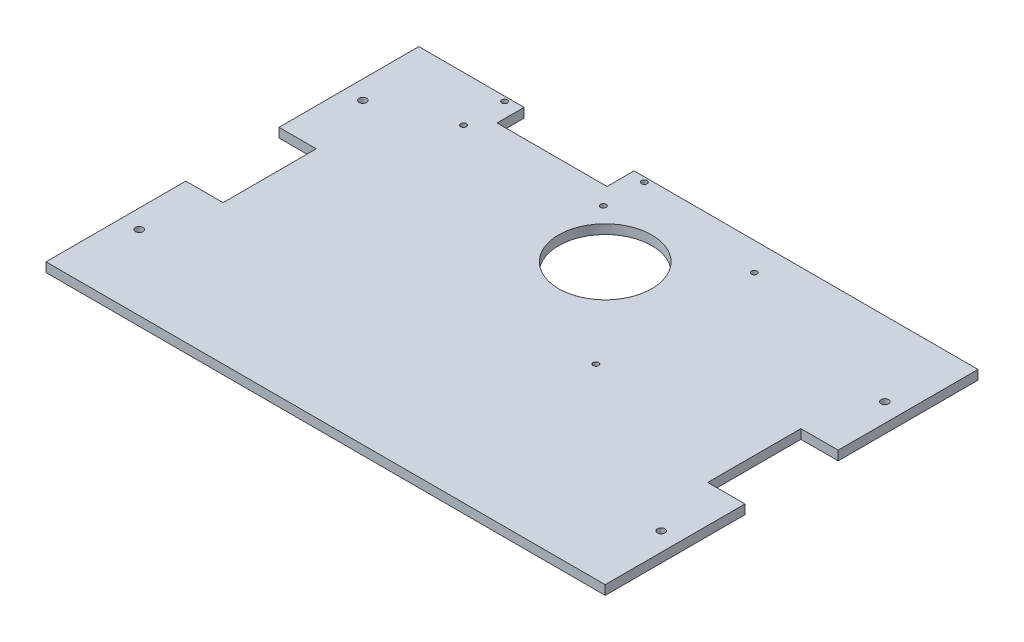
SolidWorks part; units mm, degrees
material "Glass"
ref_plane "前视基准面" through (0, 0, 0) normal (0, 0, 1) x (1, 0, 0)
ref_plane "上视基准面" through (0, 0, 0) normal (0, 1, 0) x (1, 0, 0)
ref_plane "右视基准面" through (0, 0, 0) normal (1, 0, 0) x (0, 0, -1)
sketch "Sketch1" plane through (0, 0, 0) normal (0, 1, 0) x (1, 0, 0)
  line L1 (-150, 100) -> (150, 100)
  line L2 (-150, 100) -> (-150, -100)
  line L3 (-150, -100) -> (150, -100)
  line L4 (150, 100) -> (150, -100)
  line L5 (-150, 100) -> (150, -100) construction
  line L6 (-150, -100) -> (150, 100) construction
  point P0 (0, 0)
  dimension "D1" = 200
  dimension "D2" = 300
extrude "Boss-Extrude1" add sketch "Sketch1" along normal blind 5
sketch "Sketch2" plane through (0, 5, 0) normal (0, 1, 0) x (1, 0, 0)
  line L0 (-140, 100) -> (-140, -100) construction
  line L1 (150, 100) -> (-150, 100) construction
  line L2 (-150, -100) -> (150, -100) construction
  line L3 (-150, -90) -> (150, -90) construction
  line L4 (-150, 100) -> (-150, -100) construction
  line L5 (150, -100) -> (150, 100) construction
  line L6 (0, 0) -> (0, 100) construction
  line L7 (0, 0) -> (150, 0) construction
  line L8 (140, 100) -> (140, -100) construction
  circle A0 centre (-140, 0) radius 2
  circle A1 centre (-140, 60) radius 2
  circle A5 centre (-140, -60) radius 2
  circle A7 centre (140, -60) radius 2
  circle A8 centre (140, 60) radius 2
  circle A9 centre (140, 0) radius 2
  circle A13 centre (0, 50) radius 25
  dimension "D3" = 4
  dimension "D4" = 4
  dimension "D5" = 50
  dimension "D8" = 60
  dimension "D1" = 10
  dimension "D2" = 10
extrude "Cut-Extrude2" cut sketch "Sketch2" against normal through all
sketch "Sketch4" plane through (0, 5, 0) normal (0, 1, 0) x (1, 0, 0)
  line L0 (150, 100) -> (-150, 100) construction
  line L1 (-26.5, 97.5) -> (-101.5, 97.5) construction
  line L2 (-26.5, 97.5) -> (-26.5, 75.5) construction
  line L3 (-26.5, 75.5) -> (-101.5, 75.5) construction
  line L4 (-101.5, 97.5) -> (-101.5, 75.5) construction
  line L5 (-26.5, 97.5) -> (-101.5, 75.5) construction
  line L6 (-26.5, 75.5) -> (-101.5, 97.5) construction
  line L7 (-150, 100) -> (-150, -100) construction
  circle A0 centre (-101.5, 97.5) radius 1.5
  circle A1 centre (-26.5, 97.5) radius 1.5
  circle A2 centre (-26.5, 75.5) radius 1.5
  circle A3 centre (-101.5, 75.5) radius 1.5
  point P0 (-64, 86.5)
  dimension "D3" = 3
  dimension "D1" = 75
  dimension "D2" = 22
  dimension "D4" = 2.5
  dimension "D5" = 48.5
extrude "Cut-Extrude3" cut sketch "Sketch4" against normal through all
sketch "Sketch6" plane through (0, 0, 0) normal (0, -1, 0) x (1, 0, 0)
  line L0 (150, -100) -> (-150, -100) construction
  line L1 (-93.5, -100) -> (-34.5, -100)
  line L2 (-93.5, -100) -> (-93.5, -85.5)
  line L3 (-93.5, -85.5) -> (-34.5, -85.5)
  line L4 (-34.5, -100) -> (-34.5, -85.5)
  circle A0 centre (-101.5, -75.5) radius 1.5 construction
  circle A1 centre (-26.5, -75.5) radius 1.5 construction
  dimension "D1" = 8
  dimension "D2" = 8
  dimension "D3" = 10
extrude "Cut-Extrude4" cut sketch "Sketch6" against normal blind 5
sketch "Sketch8" plane through (0, 5, 0) normal (0, 1, 0) x (1, 0, 0)
  line L0 (45, 100) -> (45, -100) construction
  line L1 (150, 100) -> (-34.5, 100) construction
  line L2 (-150, -100) -> (150, -100) construction
  line L3 (150, -100) -> (150, 100) construction
  circle A0 centre (45, 85) radius 1.5
  circle A1 centre (45, 0) radius 1.5
  dimension "D2" = 3
  dimension "D3" = 3
  dimension "D4" = 15
  dimension "D5" = 85
  dimension "D1" = 105
extrude "Cut-Extrude6" cut sketch "Sketch8" against normal through all
sketch "Sketch9" plane through (0, 5, 0) normal (0, 1, 0) x (1, 0, 0)
  line L0 (-150, 100) -> (-150, -100) construction
  line L1 (-130, -25) -> (-150, -25)
  line L2 (-130, -25) -> (-130, 25)
  line L3 (-130, 25) -> (-150, 25)
  line L4 (-150, -25) -> (-150, 25)
  line L5 (-130, -25) -> (-150, 25) construction
  line L6 (-130, 25) -> (-150, -25) construction
  line L7 (0, 0) -> (0, -100) construction
  line L8 (-150, -100) -> (150, -100) construction
  line L9 (130, 25) -> (150, -25) construction
  line L10 (130, -25) -> (150, 25) construction
  line L11 (150, -25) -> (150, 25)
  line L12 (130, 25) -> (150, 25)
  line L13 (130, -25) -> (130, 25)
  line L14 (130, -25) -> (150, -25)
  point P0 (-140, 0)
  point P17 (140, 0)
  dimension "D1" = 50
extrude "Cut-Extrude7" cut sketch "Sketch9" against normal through all
